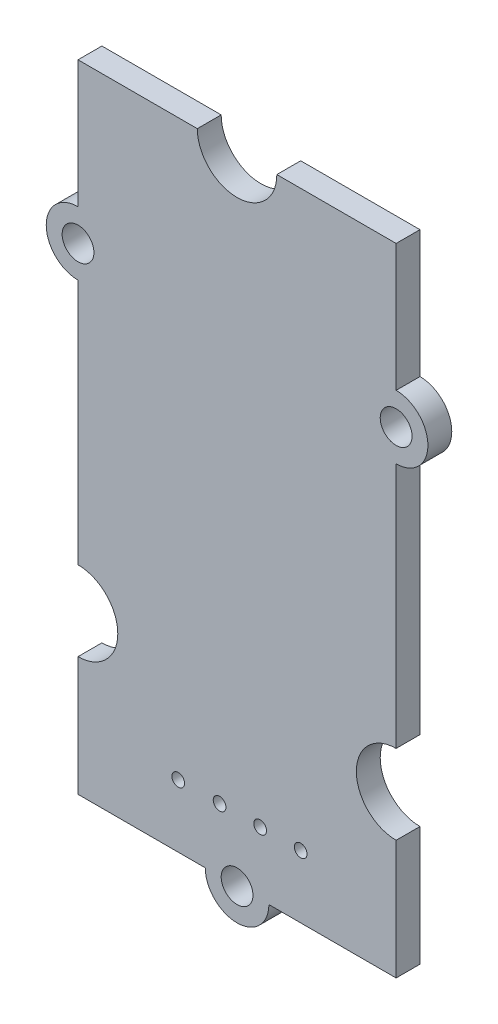
SolidWorks part; units mm, degrees
ref_plane "Plan de face" through (0, 0, 0) normal (0, 0, 1) x (1, 0, 0)
ref_plane "Plan de dessus" through (0, 0, 0) normal (0, 1, 0) x (1, 0, 0)
ref_plane "Plan de droite" through (0, 0, 0) normal (1, 0, 0) x (0, 0, -1)
sketch "Esquisse2" plane through (0, 0, 0) normal (0, 0, 1) x (1, 0, 0)
  line L0 (0, 0) -> (0, 40) construction
  line L1 (-10, 0) -> (-2, 0)
  line L2 (-10, 40) -> (-10, 32)
  line L3 (-10, 40) -> (-2.5, 40)
  line L4 (-13.2878, 30) -> (19.8637, 30) construction
  line L5 (-13.2878, 10) -> (19.8637, 10) construction
  line L6 (-10, 0) -> (-10, 40) construction
  line L7 (-10, 0) -> (-10, 7.5)
  line L8 (-10, 12.5) -> (-10, 28)
  line L9 (10, 0) -> (10, 40) construction
  line L10 (10, 12.5) -> (10, 28)
  line L11 (10, 0) -> (10, 7.5)
  line L12 (10, 40) -> (2.5, 40)
  line L13 (10, 40) -> (10, 32)
  line L14 (10, 0) -> (2, 0)
  arc A0 (-2, 0) -> (2, 0) centre (0, 0) ccw
  arc A1 (-10, 32) -> (-10, 28) centre (-10, 30) ccw
  arc A2 (-10, 12.5) -> (-10, 7.5) centre (-10, 10) cw
  arc A3 (-2.5, 40) -> (2.5, 40) centre (0, 40) ccw
  arc A4 (10, 12.5) -> (10, 7.5) centre (10, 10) ccw
  arc A5 (10, 32) -> (10, 28) centre (10, 30) cw
  dimension "D5" = 20
  dimension "D6" = 2
  dimension "D7" = 2.5
  dimension "D8" = 2.5
  dimension "D1" = 10
  dimension "D2" = 8
  dimension "D3" = 10
  dimension "D4" = 7.5
extrude "PCB" add sketch "Esquisse2" along normal blind 1.5
sketch "Esquisse3" plane through (0, 0, 1.5) normal (0, 0, 1) x (1, 0, 0)
  line L0 (-10, 40) -> (-10, 0) construction
  line L1 (-10, 30) -> (0, 30) construction
  line L2 (0, 30) -> (0, 40) construction
  line L3 (0, 40) -> (0, -2) construction
  arc A0 (-2, 0) -> (2, 0) centre (0, 0) ccw construction
  circle A1 centre (-10, 30) radius 1
  circle A2 centre (4, 3.9434) radius 0.4
  circle A3 centre (10, 30) radius 1
  circle A4 centre (0, 0) radius 1
  circle A5 centre (1.45, 3.9434) radius 0.4
  circle A6 centre (-1.1, 3.9434) radius 0.4
  circle A7 centre (-3.7, 3.9434) radius 0.4
  dimension "D1" = 2
  dimension "D2" = 2
  dimension "D3" = 4
  dimension "D4" = 1.45
  dimension "D5" = 1.1
  dimension "D6" = 3.7
extrude "Trous" cut sketch "Esquisse3" against normal through all
